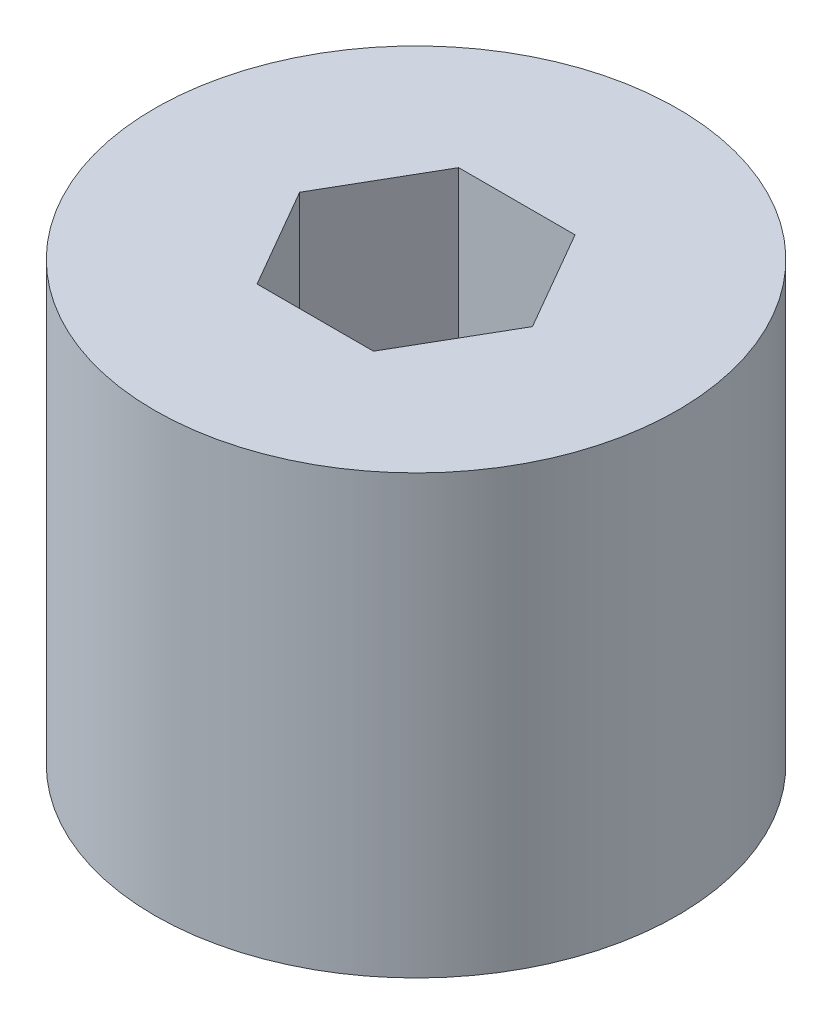
SolidWorks part; units mm, degrees
ref_plane "Front" through (0, 0, 0) normal (0, 0, 1) x (1, 0, 0)
ref_plane "Top" through (0, 0, 0) normal (0, 1, 0) x (1, 0, 0)
ref_plane "Right" through (0, 0, 0) normal (1, 0, 0) x (0, 0, -1)
sketch "Sketch1" plane through (0, 0, 0) normal (0, 1, 0) x (1, 0, 0)
  line L1 (7.7723, 0) -> (3.8861, 6.731)
  line L2 (3.8861, 6.731) -> (-3.8861, 6.731)
  line L3 (-3.8861, 6.731) -> (-7.7723, 0)
  line L4 (-7.7723, 0) -> (-3.8861, -6.731)
  line L5 (-3.8861, -6.731) -> (3.8861, -6.731)
  line L6 (3.8861, -6.731) -> (7.7723, 0)
  circle A0 centre (0, 0) radius 6.731 construction
  circle A1 centre (0, 0) radius 17.4625
  dimension "D1" = 34.925
extrude "Boss-Extrude1" add sketch "Sketch1" along normal blind 29.21
